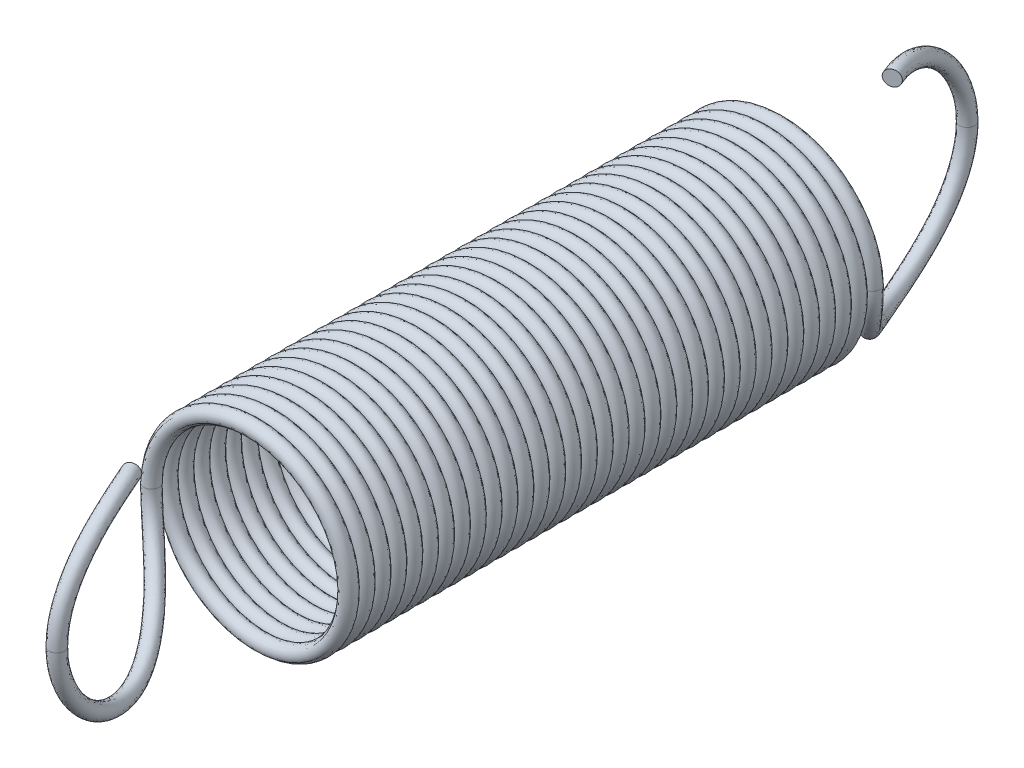
SolidWorks part; units mm, degrees
ref_plane "Front Plane" through (0, 0, 0) normal (0, 0, 1) x (1, 0, 0)
ref_plane "Top Plane" through (0, 0, 0) normal (0, 1, 0) x (1, 0, 0)
ref_plane "Right Plane" through (0, 0, 0) normal (1, 0, 0) x (0, 0, -1)
sketch "Sketch1" plane through (0, 0, 0) normal (1, 0, 0) x (0, 0, -1)
  line L0 (-8.75, 0) -> (8.75, 0) construction
  line L1 (8.75, 0) -> (53.66, 0) construction
  line L2 (-8.75, 2) -> (-8.75, -2) construction
  point P4 (0, 0)
  point P6 (-8.45, 0)
  point P9 (-8.75, 0)
  dimension "OD" = 4
  dimension "Wire Diameter" = 0.3
  dimension "Length" = 17.5
  dimension "Extended Length" = 62.41
sketch "Sketch2" plane through (0, 0, 0) normal (1, 0, 0) x (0, 0, -1)
  line L1 (-8.75, 0) -> (-9.05, 0) construction
  line L2 (-7.05, -1.7) -> (-7.05, -2) construction
  line L3 (0, 0) -> (0, 2) construction
  line L4 (-8.75, 0) -> (-8.45, 0) construction
  line L5 (-8.75, 0) -> (8.75, 0) construction
  line L6 (7.05, -1.7) -> (7.05, -2) construction
  line L7 (8.75, 0) -> (9.05, 0) construction
  line L8 (-7.05, -1.7) -> (7.05, -1.7) construction
  line L9 (-7.05, -2) -> (7.05, -2) construction
  line L10 (-5.05, 0) -> (-5.35, 0) construction
  line L11 (5.35, 0) -> (5.05, 0) construction
  line L12 (-8.75, 2) -> (-7.05, 2) construction
  circle A0 centre (-7.05, 0) radius 1.7 construction
  circle A2 centre (-7.05, 0) radius 2 construction
  circle A3 centre (7.05, 0) radius 2 construction
  circle A4 centre (7.05, 0) radius 1.7 construction
  point P7 (-3.85, 0)
  point P8 (-7.05, -1.85)
  point P10 (-8.9, 0)
  point P28 (8.9, 0)
  point P33 (-5.2, 0)
  point P34 (5.2, 0)
  point P35 (3.85, 0)
  dimension "OD" = 4
  dimension "D1" = 10.4
  dimension "D2" = 1.2
  dimension "D3" = 1.2
ref_plane "Plane1" through (0, 0, 5.2) normal (0, 0, 1) x (1, 0, 0)
sketch "Sketch3" plane through (0, 0, 5.2) normal (0, 0, 1) x (1, 0, 0)
  circle A0 centre (0, 0) radius 1.85
curve "Helix/Spiral1" pitch 0.3104 height 10.4 turns 33.5 parameters "Height"=10.4, "Pitch"=0.3104
sketch "Sketch4" plane through (0, 0, 0) normal (0, 1, 0) x (1, 0, 0)
  circle A0 centre (-1.85, -5.2) radius 0.15
  spline S0 degree 3 poles (-1.85, -5.2) (-1.85, -5.1936) (-1.7537, -5.1806) (-1.3422, -5.1612) (-0.7264, -5.1418) (0, -5.1224) (0.7264, -5.103) (1.3422, -5.0836) (1.7537, -5.0642) (1.8982, -5.0448) (1.7537, -5.0254) (1.3422, -5.006) (0.7264, -4.9866) (0, -4.9672) (-0.7264, -4.9478) (-1.3422, -4.9284) (-1.7537, -4.909) (-1.8982, -4.8896) (-1.7537, -4.8701) (-1.3422, -4.8507) (-0.7264, -4.8313) (0, -4.8119) (0.7264, -4.7925) (1.3422, -4.7731) (1.7537, -4.7537) (1.8982, -4.7343) (1.7537, -4.7149) (1.3422, -4.6955) (0.7264, -4.6761) (0, -4.6567) (-0.7264, -4.6373) (-1.3422, -4.6179) (-1.7537, -4.5985) (-1.8982, -4.5791) (-1.7537, -4.5597) (-1.3422, -4.5403) (-0.7264, -4.5209) (0, -4.5015) (0.7264, -4.4821) (1.3422, -4.4627) (1.7537, -4.4433) (1.8982, -4.4239) (1.7537, -4.4045) (1.3422, -4.3851) (0.7264, -4.3657) (0, -4.3463) (-0.7264, -4.3269) (-1.3422, -4.3075) (-1.7537, -4.2881) (-1.8982, -4.2687) (-1.7537, -4.2493) (-1.3422, -4.2299) (-0.7264, -4.2104) (0, -4.191) (0.7264, -4.1716) (1.3422, -4.1522) (1.7537, -4.1328) (1.8982, -4.1134) (1.7537, -4.094) (1.3422, -4.0746) (0.7264, -4.0552) (0, -4.0358) (-0.7264, -4.0164) (-1.3422, -3.997) (-1.7537, -3.9776) (-1.8982, -3.9582) (-1.7537, -3.9388) (-1.3422, -3.9194) (-0.7264, -3.9) (0, -3.8806) (0.7264, -3.8612) (1.3422, -3.8418) (1.7537, -3.8224) (1.8982, -3.803) (1.7537, -3.7836) (1.3422, -3.7642) (0.7264, -3.7448) (0, -3.7254) (-0.7264, -3.706) (-1.3422, -3.6866) (-1.7537, -3.6672) (-1.8982, -3.6478) (-1.7537, -3.6284) (-1.3422, -3.609) (-0.7264, -3.5896) (0, -3.5701) (0.7264, -3.5507) (1.3422, -3.5313) (1.7537, -3.5119) (1.8982, -3.4925) (1.7537, -3.4731) (1.3422, -3.4537) (0.7264, -3.4343) (0, -3.4149) (-0.7264, -3.3955) (-1.3422, -3.3761) (-1.7537, -3.3567) (-1.8982, -3.3373) (-1.7537, -3.3179) (-1.3422, -3.2985) (-0.7264, -3.2791) (0, -3.2597) (0.7264, -3.2403) (1.3422, -3.2209) (1.7537, -3.2015) (1.8982, -3.1821) (1.7537, -3.1627) (1.3422, -3.1433) (0.7264, -3.1239) (0, -3.1045) (-0.7264, -3.0851) (-1.3422, -3.0657) (-1.7537, -3.0463) (-1.8982, -3.0269) (-1.7537, -3.0075) (-1.3422, -2.9881) (-0.7264, -2.9687) (0, -2.9493) (0.7264, -2.9299) (1.3422, -2.9104) (1.7537, -2.891) (1.8982, -2.8716) (1.7537, -2.8522) (1.3422, -2.8328) (0.7264, -2.8134) (0, -2.794) (-0.7264, -2.7746) (-1.3422, -2.7552) (-1.7537, -2.7358) (-1.8982, -2.7164) (-1.7537, -2.697) (-1.3422, -2.6776) (-0.7264, -2.6582) (0, -2.6388) (0.7264, -2.6194) (1.3422, -2.6) (1.7537, -2.5806) (1.8982, -2.5612) (1.7537, -2.5418) (1.3422, -2.5224) (0.7264, -2.503) (0, -2.4836) (-0.7264, -2.4642) (-1.3422, -2.4448) (-1.7537, -2.4254) (-1.8982, -2.406) (-1.7537, -2.3866) (-1.3422, -2.3672) (-0.7264, -2.3478) (0, -2.3284) (0.7264, -2.309) (1.3422, -2.2896) (1.7537, -2.2701) (1.8982, -2.2507) (1.7537, -2.2313) (1.3422, -2.2119) (0.7264, -2.1925) (0, -2.1731) (-0.7264, -2.1537) (-1.3422, -2.1343) (-1.7537, -2.1149) (-1.8982, -2.0955) (-1.7537, -2.0761) (-1.3422, -2.0567) (-0.7264, -2.0373) (0, -2.0179) (0.7264, -1.9985) (1.3422, -1.9791) (1.7537, -1.9597) (1.8982, -1.9403) (1.7537, -1.9209) (1.3422, -1.9015) (0.7264, -1.8821) (0, -1.8627) (-0.7264, -1.8433) (-1.3422, -1.8239) (-1.7537, -1.8045) (-1.8982, -1.7851) (-1.7537, -1.7657) (-1.3422, -1.7463) (-0.7264, -1.7269) (0, -1.7075) (0.7264, -1.6881) (1.3422, -1.6687) (1.7537, -1.6493) (1.8982, -1.6299) (1.7537, -1.6104) (1.3422, -1.591) (0.7264, -1.5716) (0, -1.5522) (-0.7264, -1.5328) (-1.3422, -1.5134) (-1.7537, -1.494) (-1.8982, -1.4746) (-1.7537, -1.4552) (-1.3422, -1.4358) (-0.7264, -1.4164) (0, -1.397) (0.7264, -1.3776) (1.3422, -1.3582) (1.7537, -1.3388) (1.8982, -1.3194) (1.7537, -1.3) (1.3422, -1.2806) (0.7264, -1.2612) (0, -1.2418) (-0.7264, -1.2224) (-1.3422, -1.203) (-1.7537, -1.1836) (-1.8982, -1.1642) (-1.7537, -1.1448) (-1.3422, -1.1254) (-0.7264, -1.106) (0, -1.0866) (0.7264, -1.0672) (1.3422, -1.0478) (1.7537, -1.0284) (1.8982, -1.009) (1.7537, -0.9896) (1.3422, -0.9701) (0.7264, -0.9507) (0, -0.9313) (-0.7264, -0.9119) (-1.3422, -0.8925) (-1.7537, -0.8731) (-1.8982, -0.8537) (-1.7537, -0.8343) (-1.3422, -0.8149) (-0.7264, -0.7955) (0, -0.7761) (0.7264, -0.7567) (1.3422, -0.7373) (1.7537, -0.7179) (1.8982, -0.6985) (1.7537, -0.6791) (1.3422, -0.6597) (0.7264, -0.6403) (0, -0.6209) (-0.7264, -0.6015) (-1.3422, -0.5821) (-1.7537, -0.5627) (-1.8982, -0.5433) (-1.7537, -0.5239) (-1.3422, -0.5045) (-0.7264, -0.4851) (0, -0.4657) (0.7264, -0.4463) (1.3422, -0.4269) (1.7537, -0.4075) (1.8982, -0.3881) (1.7537, -0.3687) (1.3422, -0.3493) (0.7264, -0.3299) (0, -0.3104) (-0.7264, -0.291) (-1.3422, -0.2716) (-1.7537, -0.2522) (-1.8982, -0.2328) (-1.7537, -0.2134) (-1.3422, -0.194) (-0.7264, -0.1746) (0, -0.1552) (0.7264, -0.1358) (1.3422, -0.1164) (1.7537, -0.097) (1.8982, -0.0776) (1.7537, -0.0582) (1.3422, -0.0388) (0.7264, -0.0194) (0, 0) (-0.7264, 0.0194) (-1.3422, 0.0388) (-1.7537, 0.0582) (-1.8982, 0.0776) (-1.7537, 0.097) (-1.3422, 0.1164) (-0.7264, 0.1358) (0, 0.1552) (0.7264, 0.1746) (1.3422, 0.194) (1.7537, 0.2134) (1.8982, 0.2328) (1.7537, 0.2522) (1.3422, 0.2716) (0.7264, 0.291) (0, 0.3104) (-0.7264, 0.3299) (-1.3422, 0.3493) (-1.7537, 0.3687) (-1.8982, 0.3881) (-1.7537, 0.4075) (-1.3422, 0.4269) (-0.7264, 0.4463) (0, 0.4657) (0.7264, 0.4851) (1.3422, 0.5045) (1.7537, 0.5239) (1.8982, 0.5433) (1.7537, 0.5627) (1.3422, 0.5821) (0.7264, 0.6015) (0, 0.6209) (-0.7264, 0.6403) (-1.3422, 0.6597) (-1.7537, 0.6791) (-1.8982, 0.6985) (-1.7537, 0.7179) (-1.3422, 0.7373) (-0.7264, 0.7567) (0, 0.7761) (0.7264, 0.7955) (1.3422, 0.8149) (1.7537, 0.8343) (1.8982, 0.8537) (1.7537, 0.8731) (1.3422, 0.8925) (0.7264, 0.9119) (0, 0.9313) (-0.7264, 0.9507) (-1.3422, 0.9701) (-1.7537, 0.9896) (-1.8982, 1.009) (-1.7537, 1.0284) (-1.3422, 1.0478) (-0.7264, 1.0672) (0, 1.0866) (0.7264, 1.106) (1.3422, 1.1254) (1.7537, 1.1448) (1.8982, 1.1642) (1.7537, 1.1836) (1.3422, 1.203) (0.7264, 1.2224) (0, 1.2418) (-0.7264, 1.2612) (-1.3422, 1.2806) (-1.7537, 1.3) (-1.8982, 1.3194) (-1.7537, 1.3388) (-1.3422, 1.3582) (-0.7264, 1.3776) (0, 1.397) (0.7264, 1.4164) (1.3422, 1.4358) (1.7537, 1.4552) (1.8982, 1.4746) (1.7537, 1.494) (1.3422, 1.5134) (0.7264, 1.5328) (0, 1.5522) (-0.7264, 1.5716) (-1.3422, 1.591) (-1.7537, 1.6104) (-1.8982, 1.6299) (-1.7537, 1.6493) (-1.3422, 1.6687) (-0.7264, 1.6881) (0, 1.7075) (0.7264, 1.7269) (1.3422, 1.7463) (1.7537, 1.7657) (1.8982, 1.7851) (1.7537, 1.8045) (1.3422, 1.8239) (0.7264, 1.8433) (0, 1.8627) (-0.7264, 1.8821) (-1.3422, 1.9015) (-1.7537, 1.9209) (-1.8982, 1.9403) (-1.7537, 1.9597) (-1.3422, 1.9791) (-0.7264, 1.9985) (0, 2.0179) (0.7264, 2.0373) (1.3422, 2.0567) (1.7537, 2.0761) (1.8982, 2.0955) (1.7537, 2.1149) (1.3422, 2.1343) (0.7264, 2.1537) (0, 2.1731) (-0.7264, 2.1925) (-1.3422, 2.2119) (-1.7537, 2.2313) (-1.8982, 2.2507) (-1.7537, 2.2701) (-1.3422, 2.2896) (-0.7264, 2.309) (0, 2.3284) (0.7264, 2.3478) (1.3422, 2.3672) (1.7537, 2.3866) (1.8982, 2.406) (1.7537, 2.4254) (1.3422, 2.4448) (0.7264, 2.4642) (0, 2.4836) (-0.7264, 2.503) (-1.3422, 2.5224) (-1.7537, 2.5418) (-1.8982, 2.5612) (-1.7537, 2.5806) (-1.3422, 2.6) (-0.7264, 2.6194) (0, 2.6388) (0.7264, 2.6582) (1.3422, 2.6776) (1.7537, 2.697) (1.8982, 2.7164) (1.7537, 2.7358) (1.3422, 2.7552) (0.7264, 2.7746) (0, 2.794) (-0.7264, 2.8134) (-1.3422, 2.8328) (-1.7537, 2.8522) (-1.8982, 2.8716) (-1.7537, 2.891) (-1.3422, 2.9104) (-0.7264, 2.9299) (0, 2.9493) (0.7264, 2.9687) (1.3422, 2.9881) (1.7537, 3.0075) (1.8982, 3.0269) (1.7537, 3.0463) (1.3422, 3.0657) (0.7264, 3.0851) (0, 3.1045) (-0.7264, 3.1239) (-1.3422, 3.1433) (-1.7537, 3.1627) (-1.8982, 3.1821) (-1.7537, 3.2015) (-1.3422, 3.2209) (-0.7264, 3.2403) (0, 3.2597) (0.7264, 3.2791) (1.3422, 3.2985) (1.7537, 3.3179) (1.8982, 3.3373) (1.7537, 3.3567) (1.3422, 3.3761) (0.7264, 3.3955) (0, 3.4149) (-0.7264, 3.4343) (-1.3422, 3.4537) (-1.7537, 3.4731) (-1.8982, 3.4925) (-1.7537, 3.5119) (-1.3422, 3.5313) (-0.7264, 3.5507) (0, 3.5701) (0.7264, 3.5896) (1.3422, 3.609) (1.7537, 3.6284) (1.8982, 3.6478) (1.7537, 3.6672) (1.3422, 3.6866) (0.7264, 3.706) (0, 3.7254) (-0.7264, 3.7448) (-1.3422, 3.7642) (-1.7537, 3.7836) (-1.8982, 3.803) (-1.7537, 3.8224) (-1.3422, 3.8418) (-0.7264, 3.8612) (0, 3.8806) (0.7264, 3.9) (1.3422, 3.9194) (1.7537, 3.9388) (1.8982, 3.9582) (1.7537, 3.9776) (1.3422, 3.997) (0.7264, 4.0164) (0, 4.0358) (-0.7264, 4.0552) (-1.3422, 4.0746) (-1.7537, 4.094) (-1.8982, 4.1134) (-1.7537, 4.1328) (-1.3422, 4.1522) (-0.7264, 4.1716) (0, 4.191) (0.7264, 4.2104) (1.3422, 4.2299) (1.7537, 4.2493) (1.8982, 4.2687) (1.7537, 4.2881) (1.3422, 4.3075) (0.7264, 4.3269) (0, 4.3463) (-0.7264, 4.3657) (-1.3422, 4.3851) (-1.7537, 4.4045) (-1.8982, 4.4239) (-1.7537, 4.4433) (-1.3422, 4.4627) (-0.7264, 4.4821) (0, 4.5015) (0.7264, 4.5209) (1.3422, 4.5403) (1.7537, 4.5597) (1.8982, 4.5791) (1.7537, 4.5985) (1.3422, 4.6179) (0.7264, 4.6373) (0, 4.6567) (-0.7264, 4.6761) (-1.3422, 4.6955) (-1.7537, 4.7149) (-1.8982, 4.7343) (-1.7537, 4.7537) (-1.3422, 4.7731) (-0.7264, 4.7925) (0, 4.8119) (0.7264, 4.8313) (1.3422, 4.8507) (1.7537, 4.8701) (1.8982, 4.8896) (1.7537, 4.909) (1.3422, 4.9284) (0.7264, 4.9478) (0, 4.9672) (-0.7264, 4.9866) (-1.3422, 5.006) (-1.7537, 5.0254) (-1.8982, 5.0448) (-1.7537, 5.0642) (-1.3422, 5.0836) (-0.7264, 5.103) (0, 5.1224) (0.7264, 5.1418) (1.3422, 5.1612) (1.7537, 5.1806) (1.85, 5.1936) (1.85, 5.2) knots 0 0 0 0 0.001866 0.003731 0.005597 0.007463 0.009328 0.011194 0.01306 0.014925 0.016791 0.018657 0.020522 0.022388 0.024254 0.026119 0.027985 0.029851 0.031716 0.033582 0.035448 0.037313 0.039179 0.041045 0.04291 0.044776 0.046642 0.048507 0.050373 0.052239 0.054104 0.05597 0.057836 0.059701 0.061567 0.063433 0.065299 0.067164 0.06903 0.070896 0.072761 0.074627 0.076493 0.078358 0.080224 0.08209 0.083955 0.085821 0.087687 0.089552 0.091418 0.093284 0.095149 0.097015 0.098881 0.100746 0.102612 0.104478 0.106343 0.108209 0.110075 0.11194 0.113806 0.115672 0.117537 0.119403 0.121269 0.123134 0.125 0.126866 0.128731 0.130597 0.132463 0.134328 0.136194 0.13806 0.139925 0.141791 0.143657 0.145522 0.147388 0.149254 0.151119 0.152985 0.154851 0.156716 0.158582 0.160448 0.162313 0.164179 0.166045 0.16791 0.169776 0.171642 0.173507 0.175373 0.177239 0.179104 0.18097 0.182836 0.184701 0.186567 0.188433 0.190299 0.192164 0.19403 0.195896 0.197761 0.199627 0.201493 0.203358 0.205224 0.20709 0.208955 0.210821 0.212687 0.214552 0.216418 0.218284 0.220149 0.222015 0.223881 0.225746 0.227612 0.229478 0.231343 0.233209 0.235075 0.23694 0.238806 0.240672 0.242537 0.244403 0.246269 0.248134 0.25 0.251866 0.253731 0.255597 0.257463 0.259328 0.261194 0.26306 0.264925 0.266791 0.268657 0.270522 0.272388 0.274254 0.276119 0.277985 0.279851 0.281716 0.283582 0.285448 0.287313 0.289179 0.291045 0.29291 0.294776 0.296642 0.298507 0.300373 0.302239 0.304104 0.30597 0.307836 0.309701 0.311567 0.313433 0.315299 0.317164 0.31903 0.320896 0.322761 0.324627 0.326493 0.328358 0.330224 0.33209 0.333955 0.335821 0.337687 0.339552 0.341418 0.343284 0.345149 0.347015 0.348881 0.350746 0.352612 0.354478 0.356343 0.358209 0.360075 0.36194 0.363806 0.365672 0.367537 0.369403 0.371269 0.373134 0.375 0.376866 0.378731 0.380597 0.382463 0.384328 0.386194 0.38806 0.389925 0.391791 0.393657 0.395522 0.397388 0.399254 0.401119 0.402985 0.404851 0.406716 0.408582 0.410448 0.412313 0.414179 0.416045 0.41791 0.419776 0.421642 0.423507 0.425373 0.427239 0.429104 0.43097 0.432836 0.434701 0.436567 0.438433 0.440299 0.442164 0.44403 0.445896 0.447761 0.449627 0.451493 0.453358 0.455224 0.45709 0.458955 0.460821 0.462687 0.464552 0.466418 0.468284 0.470149 0.472015 0.473881 0.475746 0.477612 0.479478 0.481343 0.483209 0.485075 0.48694 0.488806 0.490672 0.492537 0.494403 0.496269 0.498134 0.5 0.501866 0.503731 0.505597 0.507463 0.509328 0.511194 0.51306 0.514925 0.516791 0.518657 0.520522 0.522388 0.524254 0.526119 0.527985 0.529851 0.531716 0.533582 0.535448 0.537313 0.539179 0.541045 0.54291 0.544776 0.546642 0.548507 0.550373 0.552239 0.554104 0.55597 0.557836 0.559701 0.561567 0.563433 0.565299 0.567164 0.56903 0.570896 0.572761 0.574627 0.576493 0.578358 0.580224 0.58209 0.583955 0.585821 0.587687 0.589552 0.591418 0.593284 0.595149 0.597015 0.598881 0.600746 0.602612 0.604478 0.606343 0.608209 0.610075 0.61194 0.613806 0.615672 0.617537 0.619403 0.621269 0.623134 0.625 0.626866 0.628731 0.630597 0.632463 0.634328 0.636194 0.63806 0.639925 0.641791 0.643657 0.645522 0.647388 0.649254 0.651119 0.652985 0.654851 0.656716 0.658582 0.660448 0.662313 0.664179 0.666045 0.66791 0.669776 0.671642 0.673507 0.675373 0.677239 0.679104 0.68097 0.682836 0.684701 0.686567 0.688433 0.690299 0.692164 0.69403 0.695896 0.697761 0.699627 0.701493 0.703358 0.705224 0.70709 0.708955 0.710821 0.712687 0.714552 0.716418 0.718284 0.720149 0.722015 0.723881 0.725746 0.727612 0.729478 0.731343 0.733209 0.735075 0.73694 0.738806 0.740672 0.742537 0.744403 0.746269 0.748134 0.75 0.751866 0.753731 0.755597 0.757463 0.759328 0.761194 0.76306 0.764925 0.766791 0.768657 0.770522 0.772388 0.774254 0.776119 0.777985 0.779851 0.781716 0.783582 0.785448 0.787313 0.789179 0.791045 0.79291 0.794776 0.796642 0.798507 0.800373 0.802239 0.804104 0.80597 0.807836 0.809701 0.811567 0.813433 0.815299 0.817164 0.81903 0.820896 0.822761 0.824627 0.826493 0.828358 0.830224 0.83209 0.833955 0.835821 0.837687 0.839552 0.841418 0.843284 0.845149 0.847015 0.848881 0.850746 0.852612 0.854478 0.856343 0.858209 0.860075 0.86194 0.863806 0.865672 0.867537 0.869403 0.871269 0.873134 0.875 0.876866 0.878731 0.880597 0.882463 0.884328 0.886194 0.88806 0.889925 0.891791 0.893657 0.895522 0.897388 0.899254 0.901119 0.902985 0.904851 0.906716 0.908582 0.910448 0.912313 0.914179 0.916045 0.91791 0.919776 0.921642 0.923507 0.925373 0.927239 0.929104 0.93097 0.932836 0.934701 0.936567 0.938433 0.940299 0.942164 0.94403 0.945896 0.947761 0.949627 0.951493 0.953358 0.955224 0.95709 0.958955 0.960821 0.962687 0.964552 0.966418 0.968284 0.970149 0.972015 0.973881 0.975746 0.977612 0.979478 0.981343 0.983209 0.985075 0.98694 0.988806 0.990672 0.992537 0.994403 0.996269 0.998134 1 1 1 1 construction
  dimension "D1" = 0.3
sweep "Spring Body Sweep" add profiles "Sketch4" path "Helix/Spiral1"
sketch "Sketch5" plane through (0, 0, 0) normal (1, 0, 0) x (0, 0, -1)
  line L0 (-5.35, 0) -> (-5.05, 0) construction
  line L1 (-5.35, 0) -> (-5.05, 0) construction
  line L2 (-8.75, 0) -> (8.75, 0) construction
  arc A1 (-5.2, 0) -> (-7.05, 1.85) centre (-7.05, 0) cw
sketch "Sketch6" plane through (0, 0, 0) normal (0, 1, 0) x (1, 0, 0)
  line L2 (-1.85, -5.05) -> (-1.85, -5.35) construction
  line L3 (-1.85, -5.2) -> (1.85, -5.2) construction
  line L4 (0, -8.75) -> (0, -9.05) construction
  line L5 (0, -8.9) -> (0, -5.2) construction
  arc A2 (-1.85, -5.2) -> (0, -8.9) centre (-4.625, -8.9) cw
sketch "Sketch7" plane through (0, 0, 0) normal (0, -1, 0) x (1, 0, 0)
  circle A1 centre (-1.85, 5.2) radius 0.15
  circle A3 centre (-1.85, 5.2) radius 0.15
  dimension "D1" = 0
ref_axis "Axis1" through (0, 2.5403, 0) along (0, -1, 0)
curve "Curve1"
sweep "Spring Hook Sweep" add profiles "Sketch7" path "Curve1"
pattern_circular "Spring Hook CirPattern" count 2 over 360 about axis through (0, 2.5403, 0) along (0, -1, 0) of "Spring Hook Sweep"
equation "\"D1@Sketch4\" = \"Wire Diameter@Sketch1\""
equation "\"Height@Helix/Spiral1\"=\"D1@Sketch2\""
equation "\"D2@Sketch2\" = 4 * \"Wire Diameter@Sketch1\""
equation "\"D3@Sketch2\"=\"D2@Sketch2\""
